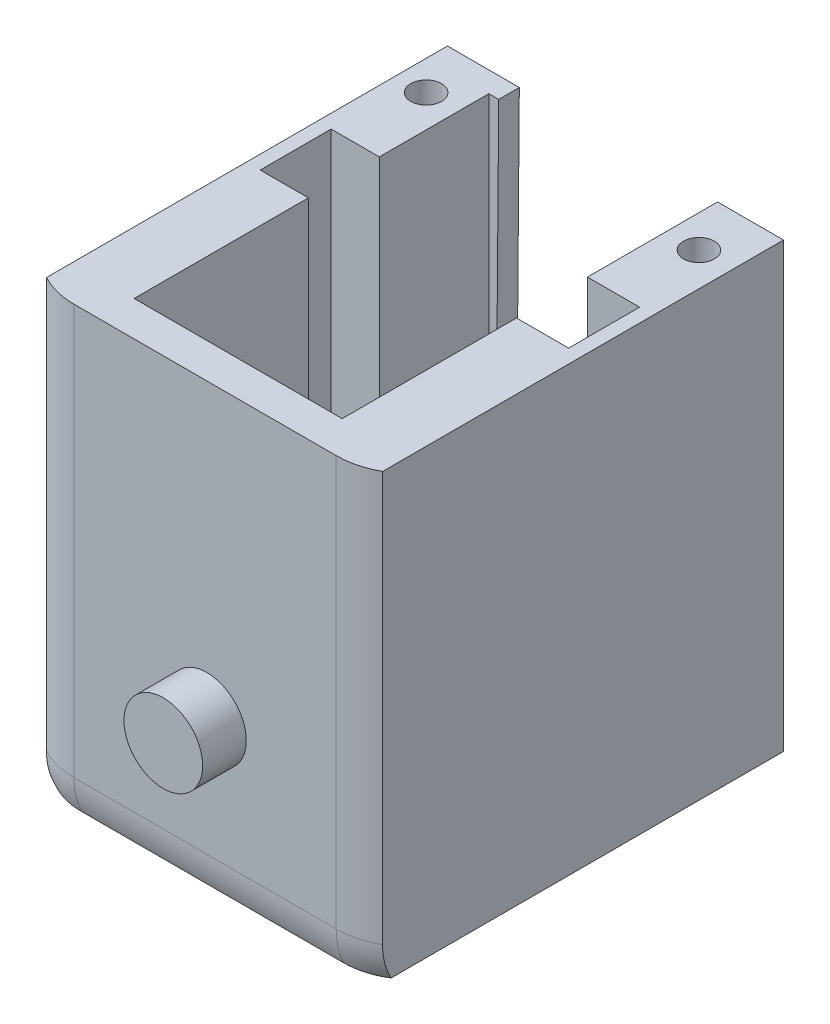
SolidWorks part; units mm, degrees
ref_plane "Alzado" through (0, 0, 0) normal (0, 0, 1) x (1, 0, 0)
ref_plane "Planta" through (0, 0, 0) normal (0, 1, 0) x (1, 0, 0)
ref_plane "Vista lateral" through (0, 0, 0) normal (1, 0, 0) x (0, 0, -1)
sketch "Sketch1" plane through (0, 0, 0) normal (0, 1, 0) x (1, 0, 0)
  line L1 (0, 0) -> (27, 0)
  line L2 (0, 0) -> (0, 32)
  line L3 (0, 32) -> (27, 32)
  line L4 (27, 0) -> (27, 32)
  dimension "D1" = 32
  dimension "D2" = 27
extrude "Boss-Extrude1" add sketch "Sketch1" along normal blind 31.58
sketch "Sketch3" plane through (0, 31.58, 0) normal (0, 1, 0) x (1, 0, 0)
  line L0 (13.5, 32) -> (13.5, 0) construction
  line L1 (27, 32) -> (0, 32) construction
  line L2 (3.5, 28.3445) -> (3.5, 5.3445)
  line L3 (3.5, 5.3445) -> (23.5, 5.3445)
  line L4 (23.5, 5.3445) -> (23.5, 28.3445)
  line L5 (23.5, 28.3445) -> (3.5, 28.3445)
  line L6 (0, 0) -> (27, 0) construction
  line L7 (27, 16) -> (0, 16) construction
  line L8 (27, 0) -> (27, 32) construction
  line L9 (0, 32) -> (0, 0) construction
  line L10 (27, 0) -> (27, 32) construction
  dimension "D2" = 23
  dimension "D3" = 3.5
extrude "Cut-Extrude1" cut sketch "Sketch3" against normal blind 30
sketch "Sketch4" plane through (0, 31.58, 0) normal (0, 1, 0) x (1, 0, 0)
  line L0 (27, 32) -> (0, 32) construction
  line L1 (9.75, 32) -> (17.25, 32)
  line L2 (9.75, 32) -> (9.75, 28.3445)
  line L3 (9.75, 28.3445) -> (17.25, 28.3445)
  line L4 (17.25, 32) -> (17.25, 28.3445)
  line L5 (23.5, 28.3445) -> (3.5, 28.3445) construction
  line L6 (13.5, 0) -> (13.5, 32) construction
  line L7 (0, 0) -> (27, 0) construction
  dimension "D1" = 7.5
extrude "Cut-Extrude2" cut sketch "Sketch4" against normal blind 25
sketch "Sketch5" plane through (0, 0, -32) normal (0, 0, -1) x (-1, 0, 0)
  circle A0 centre (-13.6189, 13.8875) radius 6.5
  circle A1 centre (-13.6189, 13.8875) radius 1.2698
  dimension "D1" = 13
extrude "Cut-Extrude4" cut sketch "Sketch5" against normal blind 10
sketch "Sketch6" plane through (0, 31.58, 0) normal (0, 1, 0) x (1, 0, 0)
  line L0 (0, 0) -> (0, 32) construction
  line L1 (0, 3.0726) -> (27, 3.0726)
  line L2 (0, 3.0726) -> (0, 0)
  line L3 (0, 0) -> (27, 0)
  line L4 (27, 3.0726) -> (27, 0)
extrude "Cut-Extrude5" cut sketch "Sketch6" against normal through all
fillet "Fillet2" radius 5 8 edges at (13.5, 0, -32) (27, 0, -17.5363) (13.5, 0, -3.0726) (0, 0, -17.5363) (0, 15.79, -3.0726) (0, 15.79, -32) (27, 15.79, -32) (27, 15.79, -3.0726)
sketch "Sketch7" plane through (0, 0, -3.0726) normal (0, 0, 1) x (1, 0, 0)
  line L2 (22, 0) -> (5, 0) construction
  circle A1 centre (13.6189, 12.657) radius 2.55
  dimension "D1" = 5.1
  dimension "D2" = 12.657
extrude "Boss-Extrude2" add sketch "Sketch7" along normal blind 2.83
sketch "Sketch8" plane through (0, 31.58, 0) normal (0, 1, 0) x (1, 0, 0)
  line L1 (23.5, 28.3445) -> (23.5, 21.2445)
  line L2 (23.5, 5.3445) -> (23.5, 28.3445) construction
  line L6 (23.5, 21.2445) -> (20.1189, 21.2445)
  line L7 (20.1189, 28.3445) -> (20.1189, 5.3445)
  line L8 (3.5, 5.3445) -> (23.5, 5.3445) construction
  line L9 (6.625, 28.3445) -> (6.625, 5.3445)
  line L10 (9.75, 28.3445) -> (3.5, 28.3445) construction
  line L11 (20.1189, 21.2445) -> (20.1189, 16.6445)
  line L12 (20.1189, 16.6445) -> (23.5, 16.6445)
  line L13 (23.5, 16.6445) -> (23.5, 5.3445)
  line L14 (23.5, 5.3445) -> (19.8211, 5.3445)
  line L15 (3.5, 5.3445) -> (23.5, 5.3445) construction
  line L16 (6.625, 21.2445) -> (3.5, 21.2445)
  line L17 (3.5, 28.3445) -> (3.5, 5.3445) construction
  line L18 (6.625, 16.6445) -> (3.5, 16.6445)
  line L19 (6.625, 5.3445) -> (3.5, 5.3445)
  line L20 (3.5, 5.3445) -> (3.5, 16.6445)
  line L21 (3.5, 21.2445) -> (3.5, 16.6445)
  line L22 (6.625, 28.3445) -> (3.5, 28.3445)
  line L23 (3.5, 28.3445) -> (3.5, 21.2445)
  line L24 (20.1189, 28.3445) -> (23.5, 28.3445)
  line L25 (23.5, 21.2445) -> (23.5, 16.6445)
  dimension "D1" = 7.1
  dimension "D2" = 4.6
extrude "Boss-Extrude4" add sketch "Sketch8" against normal blind 30
sketch "Sketch11" plane through (0, 31.58, 0) normal (0, 1, 0) x (1, 0, 0)
  line L1 (0, 32) -> (27, 32) construction
  line L2 (2.6058, 32) -> (2.6058, 3.683)
  line L3 (2.6058, 3.683) -> (0, 3.683)
  line L4 (0, 0) -> (0, 32) construction
  line L5 (0, 3.683) -> (0, 32)
  line L6 (0, 32) -> (2.6058, 32)
  line L7 (24.3942, 18.5102) -> (24.3942, 32)
  line L8 (24.3942, 32) -> (27, 32)
  line L9 (27, 32) -> (27, 2.6458)
  line L10 (27, 0) -> (27, 32) construction
  line L11 (27, 2.6458) -> (24.3942, 2.6458)
  line L12 (24.3942, 2.6458) -> (24.3942, 18.1588)
  line L13 (24.3942, 18.5102) -> (24.3942, 18.1588)
  arc A0 (0, 8.0726) -> (5, 3.0726) centre (5, 8.0726) ccw construction
extrude "Cut-Extrude10" cut sketch "Sketch11" against normal through all
sketch "Sketch12" plane through (0, 31.58, 0) normal (0, 1, 0) x (1, 0, 0)
  line L0 (2.6058, 29.6805) -> (24.3942, 29.6805)
  line L1 (2.6058, 3.683) -> (2.6058, 31.3895) construction
  line L2 (24.3942, 31.3895) -> (24.3942, 3.683) construction
  line L3 (24.3942, 29.6805) -> (24.3942, 32)
  line L4 (0, 32) -> (27, 32) construction
  line L5 (24.3942, 32) -> (2.6058, 32)
  line L6 (2.6058, 32) -> (2.6058, 29.6805)
extrude "Cut-Extrude11" cut sketch "Sketch12" against normal through all
sketch "Sketch13" plane through (0, 0, -29.6805) normal (0, 0, -1) x (-1, 0, 0)
  line L0 (-24.3942, 2.8588) -> (-2.6058, 2.8588)
  line L1 (-24.3942, 1.524) -> (-24.3942, 31.58) construction
  line L2 (-2.6058, 1.524) -> (-2.6058, 31.58) construction
  line L3 (-2.6058, 2.8588) -> (-2.6058, 0)
  line L4 (0, 0) -> (-27, 0) construction
  line L5 (-2.6058, 0) -> (-24.3942, 0)
  line L6 (-24.3942, 0) -> (-24.3942, 2.8588)
extrude "Cut-Extrude12" cut sketch "Sketch13" against normal through all
sketch "Sketch14" plane through (0, 0, -29.6805) normal (0, 0, -1) x (-1, 0, 0)
  line L0 (-20.1189, 13.8875) -> (-20.1189, 31.58)
  line L1 (-17.25, 31.58) -> (-24.3942, 31.58) construction
  line L2 (-20.1189, 2.8588) -> (-20.1189, 31.58) construction
  line L3 (-20.1189, 31.58) -> (-7.2656, 31.58)
  line L4 (-2.6058, 31.58) -> (-9.75, 31.58) construction
  line L5 (-7.2656, 31.58) -> (-7.1189, 13.8875)
  line L6 (-20.1189, 13.8875) -> (-7.1189, 13.8875)
  arc A0 (-17.25, 19.2787) -> (-17.25, 8.4963) centre (-13.6189, 13.8875) ccw construction
  arc A1 (-9.75, 8.6643) -> (-9.75, 19.1107) centre (-13.6189, 13.8875) ccw construction
extrude "Cut-Extrude13" cut sketch "Sketch14" against normal blind 10
sketch "Sketch15" plane through (0, 31.58, 0) normal (0, 1, 0) x (1, 0, 0)
  line L0 (6.625, 26.3754) -> (4.525, 26.3754)
  line L1 (6.625, 28.3445) -> (6.625, 21.2445) construction
  line L2 (20.1189, 26.3754) -> (22.2189, 26.3754)
  line L3 (20.1189, 29.6805) -> (20.1189, 21.2445) construction
  circle A0 centre (4.525, 26.3754) radius 1
  circle A1 centre (22.2189, 26.3754) radius 1
  dimension "D2" = 2
  dimension "D4" = 2
  dimension "D1" = 2.1
  dimension "D3" = 2.1
extrude "Cut-Extrude14" cut sketch "Sketch15" against normal blind 3
